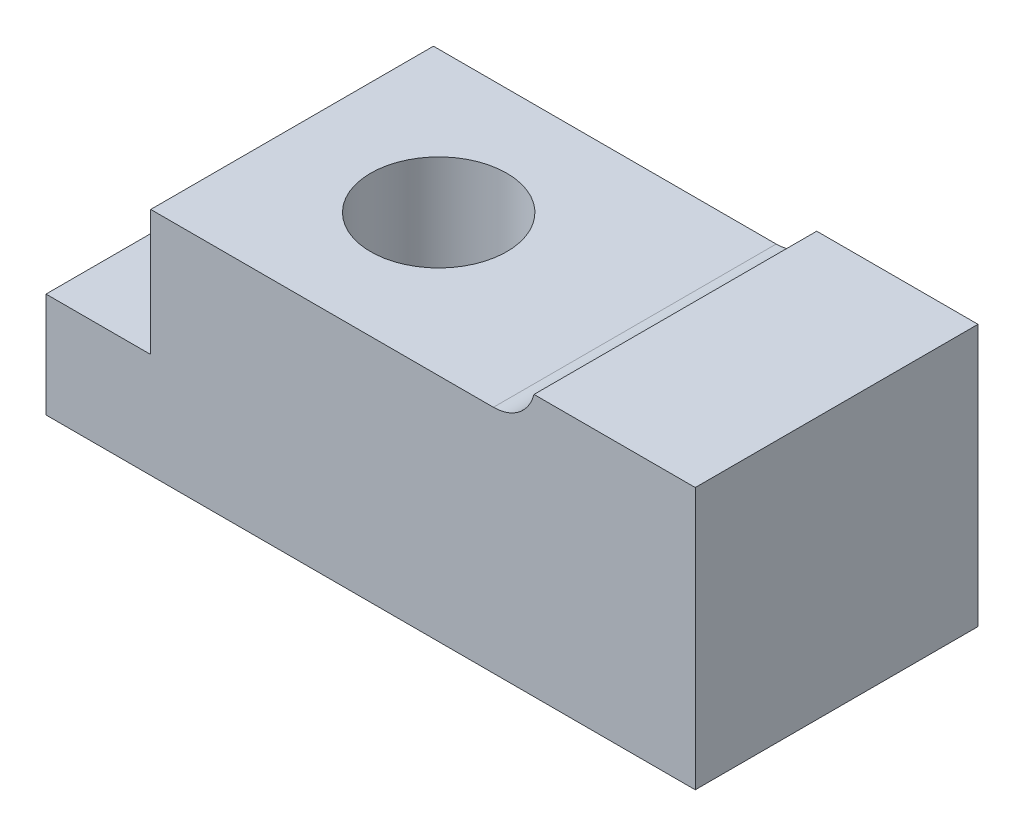
SolidWorks part; units mm, degrees
other "part"
ref_plane "Front Plane" through (0, 0, 0) normal (0, 0, 1) x (1, 0, 0)
ref_plane "Top Plane" through (0, 0, 0) normal (0, 1, 0) x (1, 0, 0)
ref_plane "Right Plane" through (0, 0, 0) normal (1, 0, 0) x (0, 0, -1)
sketch "Sketch2" plane through (0, 0, 0) normal (0, 1, 0) x (1, 0, 0)
  line L1 (31, 13.5) -> (-31, 13.5)
  line L2 (31, 13.5) -> (31, -13.5)
  line L3 (31, -13.5) -> (-31, -13.5)
  line L4 (-31, 13.5) -> (-31, -13.5)
  line L5 (31, 13.5) -> (-31, -13.5) construction
  line L6 (31, -13.5) -> (-31, 13.5) construction
  point P0 (0, 0)
  dimension "D1" = 62
  dimension "D2" = 27
extrude "Boss-Extrude1" add sketch "Sketch2" along normal blind 25
sketch "Sketch3" plane through (0, 0, 13.5) normal (0, 0, 1) x (1, 0, 0)
  line L0 (-31, 0) -> (23.6119, 0)
  line L2 (-31, 0) -> (-31, 15)
  line L3 (-31, 15) -> (-21, 15)
  line L4 (-21, 3) -> (-21, 15)
  line L7 (-21, 3) -> (23.6119, 3)
  line L8 (23.6119, 0) -> (23.6119, 3)
  dimension "D1" = 10
  dimension "D2" = 3
  dimension "D3" = 15
extrude "Cut-Extrude1" cut sketch "Sketch3" against normal through all
sketch "Sketch4" plane through (0, 25, 0) normal (0, 1, 0) x (1, 0, 0)
  line L0 (-31, 0) -> (31, 0) construction
  line L1 (-31, 13.5) -> (-31, -13.5) construction
  line L2 (31, -13.5) -> (31, 13.5) construction
  circle A0 centre (-7, 0) radius 6.5
  dimension "D1" = 13
  dimension "D2" = 24
extrude "Cut-Extrude2" cut sketch "Sketch4" against normal through all
move or copy body "Body-Move/Copy1" bodies to move or copy 103 copy no rotation origin (0, 12.5, 0) rotation axis (1, 0, 0) rotation angle 180
other "DeleteFace1" [suppressed]
other "DeleteFace2" [suppressed]
other "DeleteFace3" [suppressed]
sketch "Sketch5" plane through (0, 0, 13.5) normal (0, 0, 1) x (1, 0, 0)
  line L0 (23.6119, 25) -> (15.6, 25)
  line L1 (23.6119, 22) -> (-21, 22) construction
  line L2 (23.6119, 25) -> (23.6119, 22) construction
  line L3 (23.6119, 22) -> (11.727, 22)
  line L4 (23.6119, 25) -> (23.6119, 22)
  arc A0 (11.727, 22) -> (15.6, 25) centre (11.727, 26) ccw
  dimension "D1" = 8
  dimension "D2" = 15.4
extrude "Boss-Extrude2" add sketch "Sketch5" against normal up to surface (27 mm away) up to face at (0.653, 14.25, -13.5)
sketch "Sketch6" plane through (0, 0, 0) normal (0, -1, 0) x (1, 0, 0)
  circle A0 centre (-7, 0) radius 9.5
  dimension "D1" = 19
extrude "Cut-Extrude3" cut sketch "Sketch6" against normal blind 12
